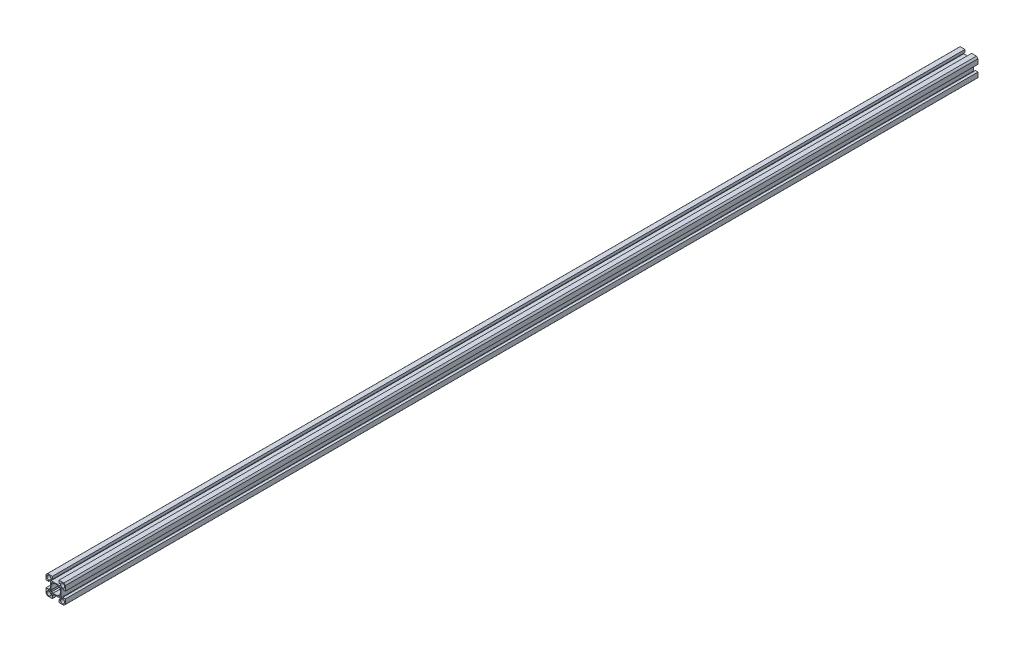
SolidWorks part; units mm, degrees
material "6063-O, Extruded Rod (SS)"
ref_plane "Front Plane" through (0, 0, 0) normal (0, 0, 1) x (1, 0, 0)
ref_plane "Top Plane" through (0, 0, 0) normal (0, 1, 0) x (1, 0, 0)
ref_plane "Right Plane" through (0, 0, 0) normal (1, 0, 0) x (0, 0, -1)
sketch "Sketch3" plane through (0, 0, 0) normal (0, 0, 1) x (1, 0, 0)
  line L0 (-7.1124, 4.5724) -> (-7.1124, -4.5724)
  line L1 (-5.334, 5.334) -> (5.334, 5.334)
  line L2 (-5.334, 5.334) -> (-5.334, -5.334)
  line L3 (-5.334, -5.334) -> (5.334, -5.334)
  line L4 (5.334, 5.334) -> (5.334, -5.334)
  line L5 (-5.334, 5.334) -> (5.334, -5.334) construction
  line L6 (-5.334, -5.334) -> (5.334, 5.334) construction
  line L7 (-4.191, 4.191) -> (4.191, 4.191)
  line L8 (-4.191, 4.191) -> (-4.191, -4.191)
  line L9 (-4.191, -4.191) -> (4.191, -4.191)
  line L10 (4.191, 4.191) -> (4.191, -4.191)
  line L11 (-4.191, 4.191) -> (4.191, -4.191) construction
  line L12 (-4.191, -4.191) -> (4.191, 4.191) construction
  line L13 (-6.9148, 6.9148) -> (6.9148, 6.9148) construction
  line L14 (-6.9148, 6.9148) -> (-6.9148, -6.9148) construction
  line L15 (-6.9148, -6.9148) -> (6.9148, -6.9148) construction
  line L16 (6.9148, 6.9148) -> (6.9148, -6.9148) construction
  line L17 (-6.9148, 6.9148) -> (6.9148, -6.9148) construction
  line L18 (-6.9148, -6.9148) -> (6.9148, 6.9148) construction
  line L19 (-3.3676, 3.3676) -> (-9.7176, 3.3676)
  line L20 (-3.3676, 3.3676) -> (-3.3676, 9.7176)
  line L21 (-3.3676, 9.7176) -> (-9.7176, 9.7176)
  line L22 (-9.7176, 3.3676) -> (-9.7176, 9.7176)
  line L23 (3.3676, 3.3676) -> (9.7176, 3.3676)
  line L24 (3.3676, 3.3676) -> (3.3676, 9.7176)
  line L25 (3.3676, 9.7176) -> (9.7176, 9.7176)
  line L26 (9.7176, 3.3676) -> (9.7176, 9.7176)
  line L27 (-3.3676, -3.3676) -> (-9.7176, -3.3676)
  line L28 (-3.3676, -3.3676) -> (-3.3676, -9.7176)
  line L29 (-3.3676, -9.7176) -> (-9.7176, -9.7176)
  line L30 (-9.7176, -3.3676) -> (-9.7176, -9.7176)
  line L31 (3.3676, -3.3676) -> (9.7176, -3.3676)
  line L32 (3.3676, -3.3676) -> (3.3676, -9.7176)
  line L33 (3.3676, -9.7176) -> (9.7176, -9.7176)
  line L34 (9.7176, -3.3676) -> (9.7176, -9.7176)
  line L35 (-9.7176, -9.7176) -> (-4.5724, -9.7176)
  line L36 (-9.7176, -9.7176) -> (-9.7176, -4.5724)
  line L37 (-9.7176, -4.5724) -> (-4.5724, -4.5724)
  line L38 (-4.5724, -9.7176) -> (-4.5724, -4.5724)
  line L39 (9.7176, -9.7176) -> (4.5724, -9.7176)
  line L40 (9.7176, -9.7176) -> (9.7176, -4.5724)
  line L41 (9.7176, -4.5724) -> (4.5724, -4.5724)
  line L42 (4.5724, -9.7176) -> (4.5724, -4.5724)
  line L43 (9.7176, 9.7176) -> (4.5724, 9.7176)
  line L44 (9.7176, 9.7176) -> (9.7176, 4.5724)
  line L45 (9.7176, 4.5724) -> (4.5724, 4.5724)
  line L46 (4.5724, 9.7176) -> (4.5724, 4.5724)
  line L47 (-9.7176, 9.7176) -> (-4.5724, 9.7176)
  line L48 (-9.7176, 9.7176) -> (-9.7176, 4.5724)
  line L49 (-9.7176, 4.5724) -> (-4.5724, 4.5724)
  line L50 (-4.5724, 9.7176) -> (-4.5724, 4.5724)
  line L51 (7.1124, 4.5724) -> (7.1124, -4.5724)
  line L52 (-4.5724, 7.1124) -> (4.5724, 7.1124)
  line L53 (-4.5724, -7.1124) -> (4.5724, -7.1124)
  circle A0 centre (0, 0) radius 4.7625
  circle A1 centre (-6.9148, 6.9148) radius 2.032
  circle A2 centre (6.9148, 6.9148) radius 2.032
  circle A3 centre (-6.9148, -6.9148) radius 2.032
  circle A4 centre (6.9148, -6.9148) radius 2.032
  circle A5 centre (0, 0) radius 12.7
  arc A6 (-9.7176, 8.1767) -> (-8.1767, 9.7176) centre (0, 0) ccw
  arc A7 (8.1767, 9.7176) -> (9.7176, 8.1767) centre (0, 0) cw
  arc A8 (9.7176, -8.1767) -> (8.1767, -9.7176) centre (0, 0) cw
  arc A9 (-8.1767, -9.7176) -> (-9.7176, -8.1767) centre (0, 0) cw
  point P0 (0, 0)
  point P6 (0, 0)
  point P47 (-8.1767, 9.7176)
  point P48 (8.1767, 9.7176)
  point P49 (-9.7176, 8.1767)
  point P50 (9.7176, 8.1767)
  point P51 (8.1767, -9.7176)
  point P52 (9.7176, -8.1767)
  point P53 (-8.1767, -9.7176)
  point P54 (-9.7176, -8.1767)
  point P74 (7.1124, 0)
  dimension "D4" = 9.525
  dimension "D6" = 4.064
  dimension "D7" = 25.4
  dimension "D1" = 10.668
  dimension "D2" = 8.382
  dimension "D3" = 10.668
  dimension "D5" = 19.558
  dimension "D8" = 6.35
  dimension "D9" = 2.54
  dimension "D10" = 2.54
  dimension "D11" = 2.54
  dimension "D12" = 2.54
extrude "Boss-Extrude3" add sketch "Sketch3" along normal blind 914.4 contours L26 A5 L25 L46 L1 L4 L45 A2 | L1 L46 L45 L4 | L46 L1 L24 L7 L10 L23 L4 L45 | A0 L7 L24 L1 L20 | A0 L10 L31 L4 L23 | L24 L52 L46 L25 | L45 L51 L23 L26 | L33 A5 L34 L41 L4 L3 L42 A4 | L42 L3 L4 L41 | L31 L51 L41 L34 | L53 L32 L33 L42 | L3 L42 L41 L4 L31 L10 L9 L32 | A0 L9 L28 L3 L32 | L3 L38 L37 L2 | L38 L3 L28 L9 L8 L27 L2 L37 | L30 A5 L29 L38 L3 L2 L37 A3 | L53 L38 L29 L28 | L30 L37 L0 L27 | A0 L8 L19 L2 L27 | L50 L1 L2 L49 | L1 L50 L49 L2 L19 L8 L7 L20 | L21 A5 L22 L49 L2 L1 L50 A1 | L50 L52 L20 L21 | L49 L22 L19 L0
